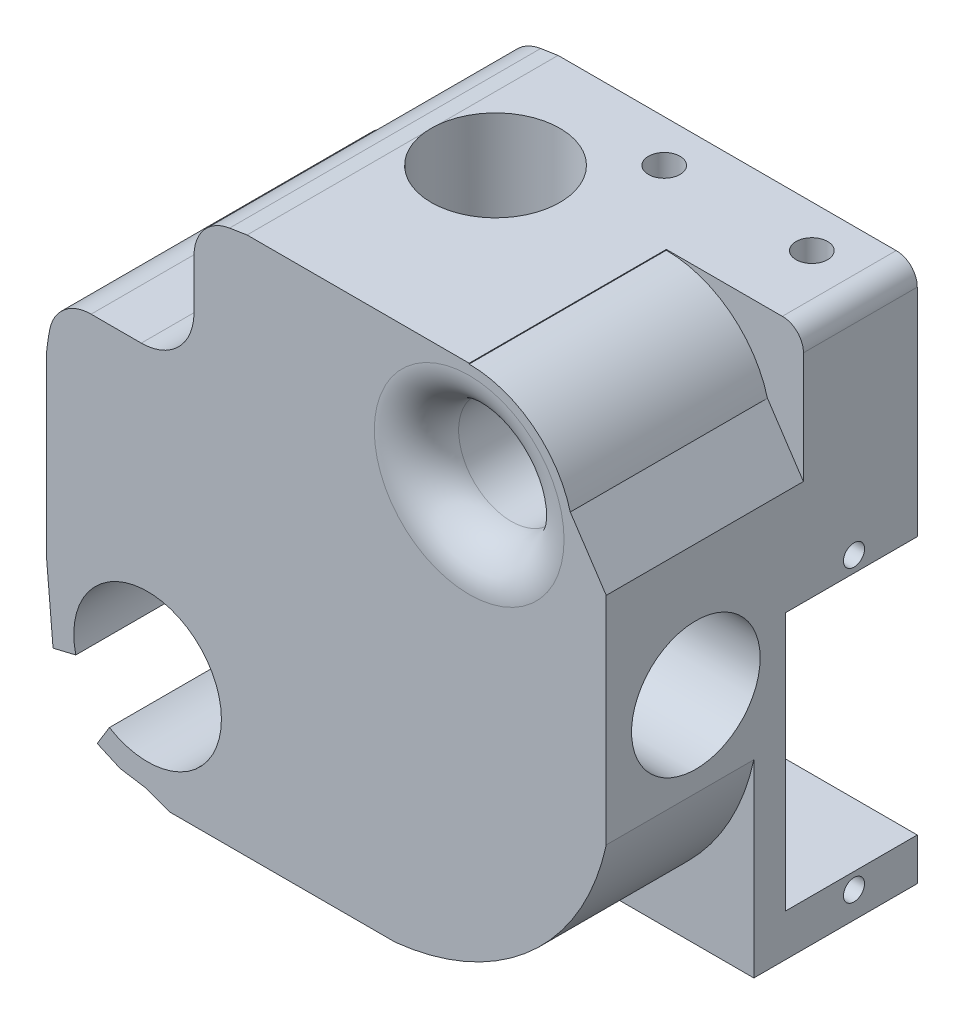
SolidWorks part; units mm, degrees
ref_plane "Alzado" through (0, 0, 0) normal (0, 0, 1) x (1, 0, 0)
ref_plane "Planta" through (0, 0, 0) normal (0, 1, 0) x (1, 0, 0)
ref_plane "Vista lateral" through (0, 0, 0) normal (1, 0, 0) x (0, 0, -1)
sketch "Croquis1" plane through (0, 0, 0) normal (0, 0, 1) x (1, 0, 0)
  line L0 (5.5323, 11.8581) -> (4.9328, 18.779)
  line L1 (4.9328, 18.779) -> (4.9328, 36)
  line L2 (9.721, 6.1246) -> (10.8757, 8.0113)
  line L3 (21.5385, 54.6227) -> (23.9328, 55)
  line L4 (58, 21.9328) -> (58, 53)
  line L6 (5.5323, 11.8581) -> (7.6906, 12.3775)
  line L7 (23.9328, 55) -> (56, 55)
  line L11 (38, 3.9328) -> (16.6419, 3.9328)
  line L12 (16.6419, 3.9328) -> (14.2653, 4.7812)
  line L13 (14.2653, 4.7812) -> (11.9047, 5.1537)
  line L14 (11.9047, 5.1537) -> (9.721, 6.1246)
  arc A0 (21.5385, 54.6227) -> (4.9328, 36) centre (26.2282, 33.726) ccw
  arc A1 (58, 53) -> (56, 55) centre (56.0336, 53.0336) ccw
  arc A2 (38, 3.9328) -> (58, 21.9328) centre (35.5538, 26.7618) ccw
  arc A3 (10.8757, 8.0113) -> (7.6906, 12.3775) centre (14.5, 14) ccw
extrude "Saliente-Extruir1" add sketch "Croquis1" against normal blind 29.5
sketch "Croquis2" plane through (0, 3.9328, 0) normal (0, -1, 0) x (1, 0, 0)
  line L0 (16.6419, -29.5) -> (16.6419, 0) construction
  line L1 (16.6419, 0) -> (38, 0) construction
  circle A0 centre (30, -17.5) radius 6.1
  dimension "D1" = 12.2
  dimension "D2" = 13.3581
  dimension "D3" = 17.5
sketch "Croquis3" plane through (0, 55, 0) normal (0, 1, 0) x (1, 0, 0)
  circle A0 centre (30, 17.5) radius 6.1
  dimension "D1" = 12.2
sketch "Croquis15" plane through (0, 0, 0) normal (0, 0, 1) x (1, 0, 0)
  line L0 (58, 42.4305) -> (58, 53)
  line L1 (45, 55) -> (56, 55)
  line L2 (45, 55) -> (45, 54.9279)
  line L5 (58, 42.4305) -> (54.5896, 47.5695)
  line L6 (58, 21.9328) -> (58, 53) construction
  line L7 (56, 55) -> (23.9328, 55) construction
  arc A0 (54.5896, 47.5695) -> (45, 54.9279) centre (45, 45) ccw
  arc A1 (58, 53) -> (56, 55) centre (56.0336, 53.0336) ccw
  arc A3 (58, 53) -> (56, 55) centre (56.0336, 53.0336) ccw construction
  dimension "D2" = 9.9279
  dimension "D1" = 0.0721
  dimension "D3" = 13
  dimension "D4" = 10
  dimension "D5" = 6.1677
  dimension "D6" = 9.4111
sketch "Croquis4" plane through (4.9328, 0, 0) normal (-1, 0, 0) x (0, 0, 1)
  line L0 (0, 36) -> (0, 18.779) construction
  line L1 (-29.5, 36) -> (0, 36) construction
  circle A0 centre (-8.5, 30) radius 6.1
  dimension "D1" = 12.2
  dimension "D2" = 8.5
  dimension "D3" = 6
sketch "Croquis5" plane through (58, 0, 0) normal (1, 0, 0) x (0, 0, -1)
  circle A0 centre (8.5, 30) radius 6.1
  dimension "D1" = 12.2
sketch "Croquis6" plane through (0, 0, -29.5) normal (0, 0, -1) x (-1, 0, 0)
  line L0 (-4.9328, 36) -> (-4.9328, 18.779) construction
  line L1 (-56, 55) -> (-23.9328, 55) construction
  circle A0 centre (-45, 45) radius 8.5
  dimension "D1" = 17
  dimension "D2" = 40.0672
  dimension "D3" = 10
extrude "Cortar-Extruir11" cut sketch "Croquis15" against normal blind 18.7
sketch "Croquis12" plane through (0, 0, -29.5) normal (0, 0, -1) x (-1, 0, 0)
  line L0 (-4.9328, 36) -> (-4.9328, 18.779) construction
  line L1 (-58, 4) -> (-38, 4)
  line L2 (-58, 4) -> (-58, 32.5)
  line L3 (-58, 32.5) -> (-38, 32.5)
  line L4 (-38, 4) -> (-38, 32.5)
  line L5 (-56, 55) -> (-23.9328, 55) construction
  dimension "D1" = 33.0672
  dimension "D2" = 53.0672
  dimension "D3" = 22.5
  dimension "D4" = 51
extrude "Saliente-Extruir2" add sketch "Croquis12" against normal blind 15.5
extrude "Cortar-Extruir1" cut sketch "Croquis6" against normal blind 10
sketch "Croquis7" plane through (0, 0, -19.5) normal (0, 0, -1) x (-1, 0, 0)
  circle A0 centre (-45, 45) radius 4.1
  circle A1 centre (-45, 45) radius 8.5 construction
  dimension "D1" = 8.2
extrude "Cortar-Extruir2" cut sketch "Croquis7" against normal blind 13.5
sketch "Croquis8" plane through (0, 0, 0) normal (0, 0, 1) x (1, 0, 0)
  line L0 (4.9328, 36) -> (4.9328, 18.779) construction
  line L1 (45, 55) -> (23.9328, 55) construction
  circle A0 centre (45, 45) radius 4.4
  dimension "D1" = 8.8
  dimension "D2" = 40.0672
  dimension "D3" = 10
extrude "Cortar-Extruir3" cut sketch "Croquis8" against normal blind 6
extrude "Cortar-Extruir4" cut sketch "Croquis2" against normal blind 20
extrude "Cortar-Extruir5" cut sketch "Croquis3" against normal blind 20
extrude "Cortar-Extruir6" cut sketch "Croquis4" against normal blind 20
extrude "Cortar-Extruir7" cut sketch "Croquis5" against normal blind 20
sketch "Croquis9" plane through (38, 0, 0) normal (1, 0, 0) x (0, 0, -1)
  circle A0 centre (8.5, 30) radius 3.5
  circle A1 centre (8.5, 30) radius 6.1 construction
  dimension "D1" = 7
extrude "Cortar-Extruir8" cut sketch "Croquis9" against normal up to next
sketch "Croquis10" plane through (0, 23.9328, 0) normal (0, -1, 0) x (1, 0, 0)
  circle A0 centre (30, -17.5) radius 3.5
  circle A1 centre (30, -17.5) radius 6.1 construction
  dimension "D1" = 7
extrude "Cortar-Extruir9" cut sketch "Croquis10" against normal up to next
sketch "Croquis13" plane through (0, 0, -29.5) normal (0, 0, -1) x (-1, 0, 0)
  line L0 (-58, 4) -> (-58, 53) construction
  line L1 (-58, 8) -> (-38, 8)
  line L2 (-58, 8) -> (-58, 32.5)
  line L3 (-58, 32.5) -> (-38, 32.5)
  line L4 (-38, 8) -> (-38, 32.5)
  line L5 (-16.6419, 3.9328) -> (-38, 3.9328) construction
  dimension "D1" = 20
  dimension "D2" = 4.0672
  dimension "D3" = 28.5672
extrude "Cortar-Extruir10" cut sketch "Croquis13" against normal blind 12.5
sketch "Croquis18" plane through (0, 55, 0) normal (0, 1, 0) x (1, 0, 0)
  line L0 (23.9328, 16.8687) -> (23.9328, 0) construction
  line L1 (45, 0) -> (23.9328, 0) construction
  circle A0 centre (38, 25.5) radius 1.5
  circle A1 centre (52, 25.5) radius 1.5
  dimension "D1" = 3
  dimension "D2" = 3
  dimension "D3" = 14.0672
  dimension "D4" = 28.0672
  dimension "D5" = 25.5
extrude "Cortar-Extruir12" cut sketch "Croquis18" against normal up to next
sketch "Croquis19" plane through (58, 0, 0) normal (1, 0, 0) x (0, 0, -1)
  line L0 (29.5, 53) -> (18.7, 53) construction
  line L1 (29.5, 32.5) -> (29.5, 53) construction
  circle A0 centre (23.5, 34) radius 1
  circle A1 centre (23.5, 6.5) radius 1
  dimension "D1" = 2
  dimension "D2" = 2
  dimension "D3" = 6
  dimension "D4" = 19
  dimension "D5" = 46.5
extrude "Cortar-Extruir13" cut sketch "Croquis19" against normal blind 10
sketch "Croquis20" plane through (0, 0, -29.5) normal (0, 0, -1) x (-1, 0, 0)
  line L0 (-58, 4) -> (-58, 8) construction
  line L1 (-16.6419, 3.9328) -> (-38, 3.9328) construction
  circle A0 centre (-16, 36) radius 2.1
  dimension "D1" = 4.2
extrude "Cortar-Extruir14" cut sketch "Croquis20" against normal blind 10
sketch "Croquis21" plane through (0, 0, 0) normal (0, 0, 1) x (1, 0, 0)
  circle A0 centre (45, 45) radius 5
  dimension "D1" = 10
extrude "Cortar-Extruir15" cut sketch "Croquis21" against normal blind 50
sketch "Croquis23" plane through (0, 0, 0) normal (0, 0, 1) x (1, 0, 0)
  line L0 (24.9328, 36.1) -> (4.9437, 36.1) construction
  line L1 (18.9, 55.5238) -> (2.3751, 55.5238)
  line L2 (18.9, 55.5238) -> (18.9, 41.1)
  line L3 (18.9, 41.1) -> (2.3751, 41.1)
  line L4 (2.3751, 55.5238) -> (2.3751, 41.1)
  line L5 (23.9, 55) -> (23.9, 35) construction
  dimension "D1" = 5
  dimension "D2" = 5
extrude "Cortar-Extruir16" cut sketch "Croquis23" against normal blind 50
fillet "Redondeo1" radius 4 2 edges at (6.1212, 41.1, -14.75) (18.9, 53.8497, -14.75)
fillet "Redondeo2" radius 5 1 edges at (18.9, 41.1, -14.75)
fillet "Redondeo3" radius 4 1 edges at (50, 45, 0)
